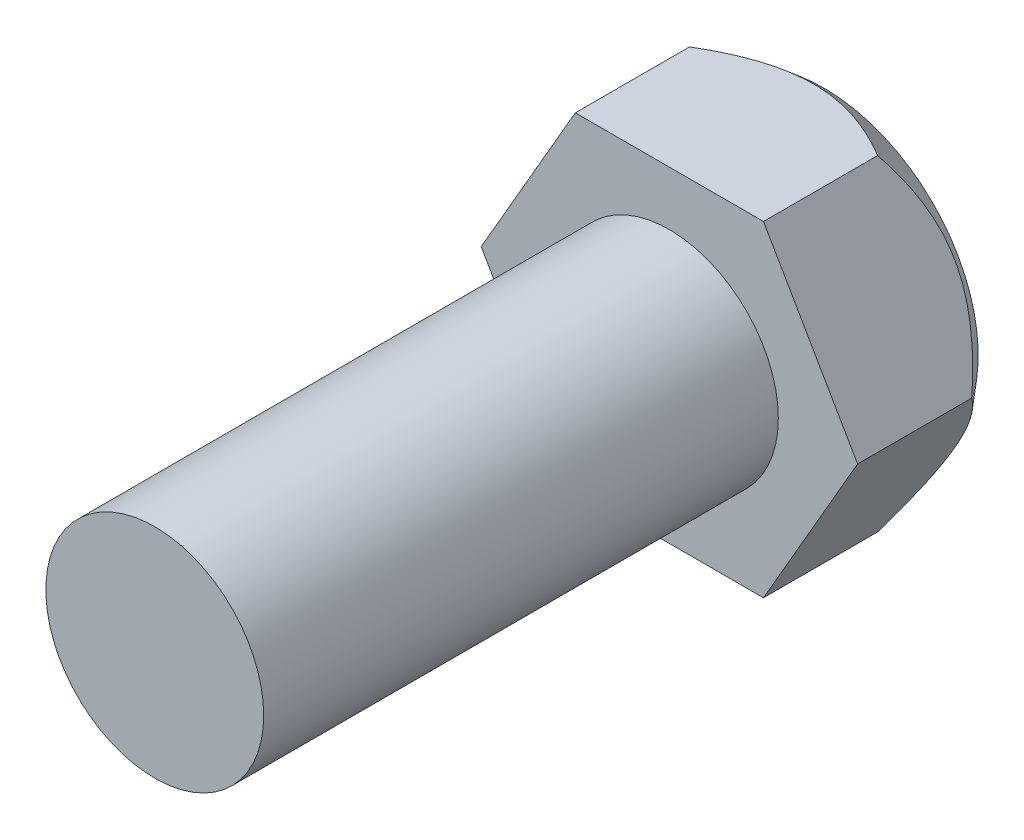
SolidWorks part; units mm, degrees
ref_plane "Alzado" through (0, 0, 0) normal (0, 0, 1) x (1, 0, 0)
ref_plane "Planta" through (0, 0, 0) normal (0, 1, 0) x (1, 0, 0)
ref_plane "Vista lateral" through (0, 0, 0) normal (1, 0, 0) x (0, 0, -1)
sketch "Croquis1" plane through (0, 0, 0) normal (0, 0, 1) x (1, 0, 0)
  line L1 (10.9697, 0) -> (5.4848, 9.5)
  line L2 (5.4848, 9.5) -> (-5.4848, 9.5)
  line L3 (-5.4848, 9.5) -> (-10.9697, 0)
  line L4 (-10.9697, 0) -> (-5.4848, -9.5)
  line L5 (-5.4848, -9.5) -> (5.4848, -9.5)
  line L6 (5.4848, -9.5) -> (10.9697, 0)
  circle A0 centre (0, 0) radius 9.5 construction
  dimension "D1" = 19
extrude "Saliente-Extruir1" add sketch "Croquis1" along normal blind 9
sketch "Croquis2" plane through (0, 0, 9) normal (0, 0, 1) x (1, 0, 0)
  circle A0 centre (0, 0) radius 6.35
  dimension "D1" = 12.7
extrude "Saliente-Extruir2" add sketch "Croquis2" along normal blind 30
sketch "Croquis3" plane through (0, 0, 0) normal (0, 0, -1) x (-1, 0, 0)
  circle A0 centre (0, 0) radius 9
  circle A1 centre (0, 0) radius 18.8146
extrude "Cortar-Extruir1" cut sketch "Croquis3" against normal blind 10 draft 40
